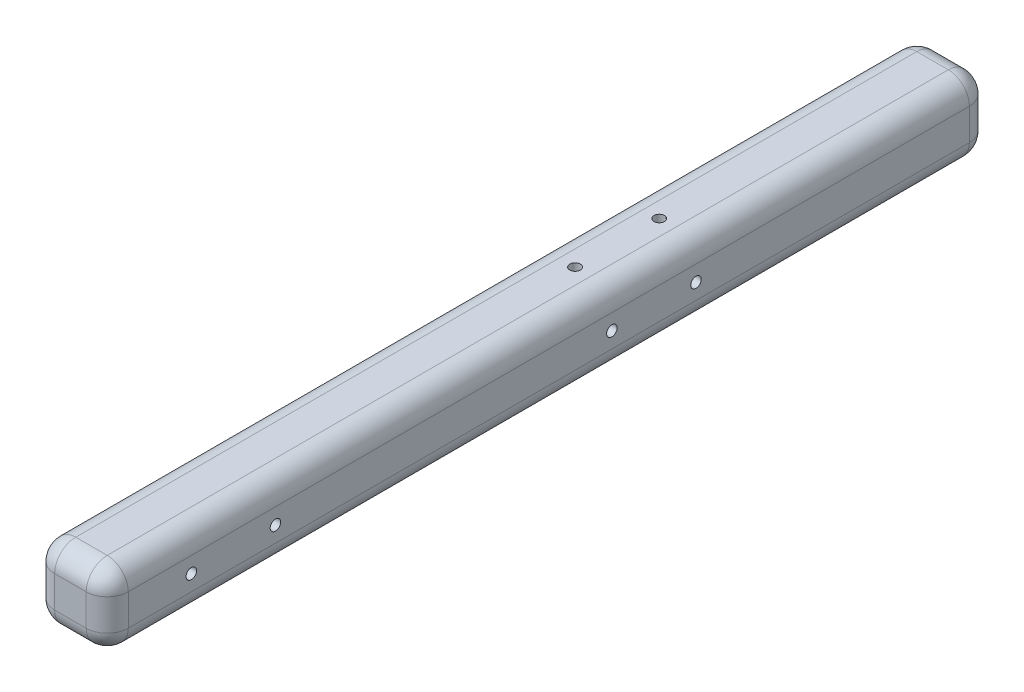
SolidWorks part; units mm, degrees
material "Pine"
ref_plane "Front Plane" through (0, 0, 0) normal (0, 0, 1) x (1, 0, 0)
ref_plane "Top Plane" through (0, 0, 0) normal (0, 1, 0) x (1, 0, 0)
ref_plane "Right Plane" through (0, 0, 0) normal (1, 0, 0) x (0, 0, -1)
sketch "Sketch1" plane through (0, 0, 0) normal (0, 0, 1) x (1, 0, 0)
  line L1 (-9.525, -22.225) -> (9.525, -22.225)
  line L2 (-22.225, -9.525) -> (-22.225, 9.525)
  line L3 (-9.525, 22.225) -> (9.525, 22.225)
  line L4 (22.225, -9.525) -> (22.225, 9.525)
  line L5 (-22.225, -22.225) -> (22.225, 22.225) construction
  line L6 (-22.225, 22.225) -> (22.225, -22.225) construction
  arc A0 (-9.525, -22.225) -> (-22.225, -9.525) centre (-9.525, -9.525) cw
  arc A1 (22.225, -9.525) -> (9.525, -22.225) centre (9.525, -9.525) cw
  arc A2 (22.225, 9.525) -> (9.525, 22.225) centre (9.525, 9.525) ccw
  arc A3 (-9.525, 22.225) -> (-22.225, 9.525) centre (-9.525, 9.525) ccw
  point P0 (0, 0)
  dimension "D3" = 12.7
  dimension "D1" = 44.45
  dimension "D2" = 44.45
extrude "Boss-Extrude1" add sketch "Sketch1" along normal blind 254
fillet "Fillet1" radius 12.7 8 edges at (18.5053, 18.5053, 0) (22.225, 0, 0) (18.5053, -18.5053, 0) (0, -22.225, 0) (-18.5053, -18.5053, 0) (-22.225, 0, 0) (-18.5053, 18.5053, 0) (0, 22.225, 0)
sketch "Sketch2" plane through (0, 22.225, 0) normal (0, 1, 0) x (1, 0, 0)
  line L0 (0, -1210.9207) -> (0, 48789.0793) construction
  line L2 (-1047.1464, -228.6) -> (48952.8536, -228.6) construction
  line L3 (-1039.9802, -177.8) -> (48960.0198, -177.8) construction
  line L4 (9.525, -254) -> (-9.525, -254) construction
  circle A0 centre (0, -177.8) radius 3.175
  circle A1 centre (0, -228.6) radius 3.175
  dimension "D3" = 6.35
  dimension "D4" = 6.35
  dimension "D1" = 25.4
  dimension "D2" = 50.8
extrude "Cut-Extrude1" cut sketch "Sketch2" against normal blind 12.7
sketch "Sketch3" plane through (0, 0, 0) normal (0, 1, 0) x (1, 0, 0)
  line L0 (0, -1052.1314) -> (0, 48947.8686) construction
pattern_circular "CirPattern2" count 2 every 90 about axis through (0, 0, 1052.1314) along (0, 0, -1) of "Cut-Extrude1"
sketch "Sketch4" plane through (0, 0, 254) normal (0, 0, 1) x (1, 0, 0)
  line L1 (-9.525, -22.225) -> (9.525, -22.225)
  line L2 (-22.225, -9.525) -> (-22.225, 9.525)
  line L3 (-9.525, 22.225) -> (9.525, 22.225)
  line L4 (22.225, -9.525) -> (22.225, 9.525)
  line L5 (-22.225, -22.225) -> (22.225, 22.225) construction
  line L6 (-22.225, 22.225) -> (22.225, -22.225) construction
  arc A0 (-9.525, -22.225) -> (-22.225, -9.525) centre (-9.525, -9.525) cw
  arc A1 (22.225, -9.525) -> (9.525, -22.225) centre (9.525, -9.525) cw
  arc A2 (22.225, 9.525) -> (9.525, 22.225) centre (9.525, 9.525) ccw
  arc A3 (-9.525, 22.225) -> (-22.225, 9.525) centre (-9.525, 9.525) ccw
  point P0 (0, 0)
  dimension "D3" = 12.7
  dimension "D1" = 44.45
  dimension "D2" = 44.45
extrude "Boss-Extrude2" add sketch "Sketch4" along normal blind 279.4
fillet "Fillet2" radius 12.7 8 edges at (18.5053, -18.5053, 533.4) (0, -22.225, 533.4) (-18.5053, -18.5053, 533.4) (-22.225, 0, 533.4) (-18.5053, 18.5053, 533.4) (0, 22.225, 533.4) (18.5053, 18.5053, 533.4) (22.225, 0, 533.4)
sketch "Sketch5" plane through (22.225, 0, 0) normal (1, 0, 0) x (0, 0, -1)
  line L0 (-1468.208, 0) -> (48531.792, 0) construction
  line L2 (-482.6, -973.3013) -> (-482.6, 49026.6987) construction
  line L3 (-431.8, -973.3013) -> (-431.8, 49026.6987) construction
  line L4 (-533.4, -9.525) -> (-533.4, 9.525) construction
  circle A0 centre (-431.8, 0) radius 3.175
  circle A1 centre (-482.6, 0) radius 3.175
  dimension "D3" = 6.35
  dimension "D4" = 6.35
  dimension "D1" = 50.8
  dimension "D2" = 50.8
extrude "Cut-Extrude2" cut sketch "Sketch5" against normal blind 12.7
